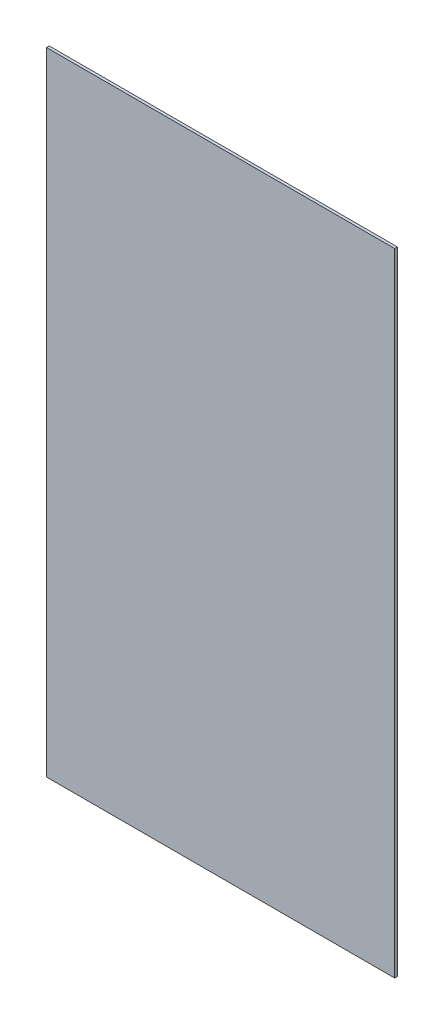
SolidWorks part; units mm, degrees
ref_plane "Front" through (0, 0, 0) normal (0, 0, 1) x (1, 0, 0)
ref_plane "Top" through (0, 0, 0) normal (0, 1, 0) x (1, 0, 0)
ref_plane "Right" through (0, 0, 0) normal (1, 0, 0) x (0, 0, -1)
sketch "Sketch1" plane through (0, 0, 0) normal (0, 0, 1) x (1, 0, 0)
  line L0 (266.7, 0) -> (266.7, 1095.375) construction
  line L1 (-34.925, 0) -> (568.325, 0)
  line L2 (-34.925, 0) -> (-34.925, 1095.375)
  line L3 (-34.925, 1095.375) -> (568.325, 1095.375)
  line L4 (568.325, 0) -> (568.325, 1095.375)
  line L5 (266.7, 547.6875) -> (-34.925, 547.6875) construction
  line L6 (266.7, 547.6875) -> (568.325, 547.6875) construction
  dimension "D1" = 1095.375
  dimension "D2" = 603.25
extrude "Extrude1" add sketch "Sketch1" along normal blind 4.7625
